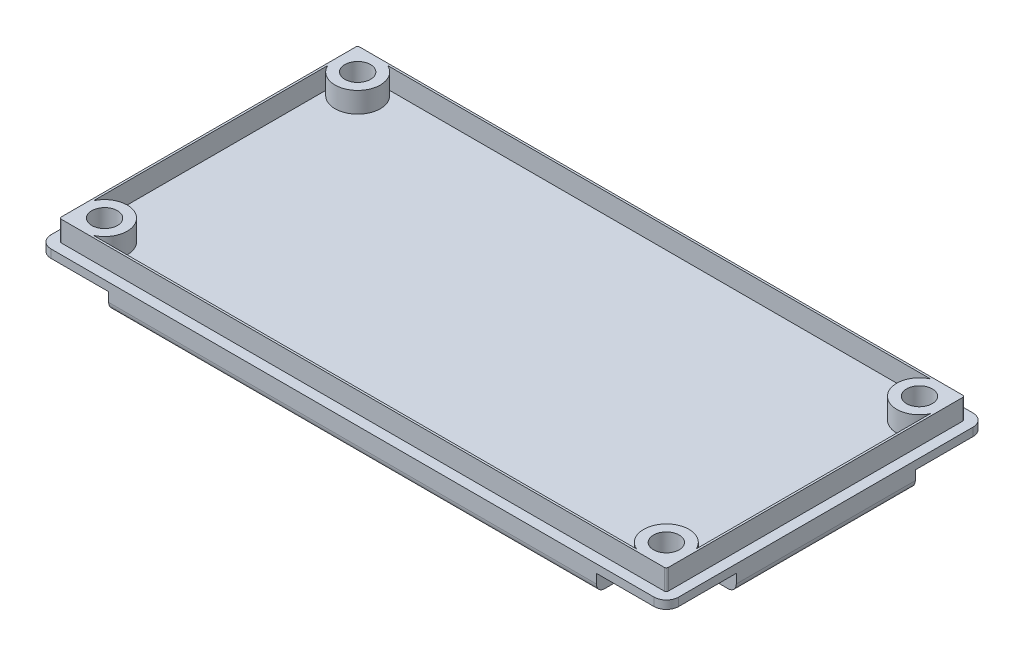
SolidWorks part; units mm, degrees
material "ABS"
ref_plane "Front Plane" through (0, 0, 0) normal (0, 0, 1) x (1, 0, 0)
ref_plane "Top Plane" through (0, 0, 0) normal (0, 1, 0) x (1, 0, 0)
ref_plane "Right Plane" through (0, 0, 0) normal (1, 0, 0) x (0, 0, -1)
sketch "Sketch1" plane through (0, 0, 0) normal (0, 1, 0) x (1, 0, 0)
  line L0 (-19.3675, 0) -> (19.3675, 0) construction
  line L1 (-18.6055, 9.8425) -> (18.6055, 9.8425)
  line L2 (-19.3675, 9.0805) -> (-19.3675, -9.0805)
  line L3 (-18.6055, -9.8425) -> (18.6055, -9.8425)
  line L4 (19.3675, 9.0805) -> (19.3675, -9.0805)
  line L5 (0, -9.8425) -> (0, 9.8425) construction
  line L8 (19.3675, 9.0805) -> (19.3675, -9.0805) construction
  line L9 (18.6055, -9.8425) -> (-18.6055, -9.8425) construction
  arc A0 (-18.6055, -9.8425) -> (-19.3675, -9.0805) centre (-18.6055, -9.0805) cw
  arc A1 (18.6055, -9.8425) -> (19.3675, -9.0805) centre (18.6055, -9.0805) ccw
  arc A2 (19.3675, 9.0805) -> (18.6055, 9.8425) centre (18.6055, 9.0805) ccw
  arc A3 (-19.3675, 9.0805) -> (-18.6055, 9.8425) centre (-18.6055, 9.0805) cw
  circle A4 centre (-17.3355, 7.8105) radius 0.7937
  circle A5 centre (17.3355, 7.8105) radius 0.7937
  circle A6 centre (17.3355, -7.8105) radius 0.7937
  circle A7 centre (-17.3355, -7.8105) radius 0.7937
  arc A9 (-19.3675, -9.0805) -> (-18.6055, -9.8425) centre (-18.6055, -9.0805) ccw construction
  circle A10 centre (17.3355, -7.8105) radius 0.7937 construction
extrude "Extrude1" add sketch "Sketch1" along normal blind 1.5875
fillet "Fillet2" radius 0.508 8 edges at (19.1443, 0, -9.6193) (19.3675, 0, 0) (19.1443, 0, 9.6193) (0, 0, 9.8425) (-19.1443, 0, 9.6193) (-19.3675, 0, 0) (-19.1443, 0, -9.6193) (0, 0, -9.8425)
sketch "Sketch2" plane through (0, 1.5875, 0) normal (0, 1, 0) x (-1, 0, 0)
  line L4 (-18.6055, -7.2285) -> (-18.6055, 7.2285)
  line L5 (-16.7535, 9.0805) -> (16.7535, 9.0805)
  line L6 (18.6055, 7.2285) -> (18.6055, -7.2285)
  line L7 (16.7535, -9.0805) -> (-16.7535, -9.0805)
  line L8 (18.6055, 9.2075) -> (-18.6055, 9.2075)
  line L9 (-18.7325, 9.0805) -> (-18.7325, -9.0805)
  line L10 (-18.6055, -9.2075) -> (18.6055, -9.2075)
  line L11 (18.7325, -9.0805) -> (18.7325, 9.0805)
  line L12 (18.6055, 9.2075) -> (-18.6055, 9.2075)
  line L13 (-18.7325, 9.0805) -> (-18.7325, -9.0805)
  line L14 (-18.6055, -9.2075) -> (18.6055, -9.2075)
  line L15 (18.7325, -9.0805) -> (18.7325, 9.0805)
  circle A4 centre (-17.3355, 7.8105) radius 0.7938 construction
  circle A5 centre (-17.3355, -7.8105) radius 0.7937 construction
  circle A6 centre (17.3355, -7.8105) radius 0.7937 construction
  circle A7 centre (17.3355, 7.8105) radius 0.7938 construction
  arc A8 (18.7325, 9.0805) -> (18.6055, 9.2075) centre (18.6055, 9.0805) ccw
  arc A9 (-18.6055, 9.2075) -> (-18.7325, 9.0805) centre (-18.6055, 9.0805) ccw
  arc A10 (-18.7325, -9.0805) -> (-18.6055, -9.2075) centre (-18.6055, -9.0805) ccw
  arc A11 (18.6055, -9.2075) -> (18.7325, -9.0805) centre (18.6055, -9.0805) ccw
  arc A12 (18.7325, 9.0805) -> (18.6055, 9.2075) centre (18.6055, 9.0805) ccw
  arc A13 (-18.6055, 9.2075) -> (-18.7325, 9.0805) centre (-18.6055, 9.0805) ccw
  arc A14 (-18.7325, -9.0805) -> (-18.6055, -9.2075) centre (-18.6055, -9.0805) ccw
  arc A15 (18.6055, -9.2075) -> (18.7325, -9.0805) centre (18.6055, -9.0805) ccw
  circle A16 centre (-17.3355, 7.8105) radius 0.7937
  circle A17 centre (-17.3355, -7.8105) radius 0.7937
  circle A18 centre (17.3355, -7.8105) radius 0.7937
  circle A19 centre (17.3355, 7.8105) radius 0.7937
  arc A20 (-16.7535, -9.0805) -> (-18.6055, -7.2285) centre (-17.3355, -7.8105) ccw
  arc A21 (16.7535, 9.0805) -> (18.6055, 7.2285) centre (17.3355, 7.8105) ccw
  arc A22 (18.6055, -7.2285) -> (16.7535, -9.0805) centre (17.3355, -7.8105) ccw
  arc A23 (-18.6055, 7.2285) -> (-16.7535, 9.0805) centre (-17.3355, 7.8105) ccw
  dimension "D1" = 0.635
extrude "Extrude2" add sketch "Sketch2" along normal blind 1.27
sketch "Sketch3" plane through (0, 0, 0) normal (0, -1, 0) x (1, 0, 0)
  line L0 (18.6055, -9.8425) -> (-18.6055, -9.8425) construction
  line L1 (-16.3195, -5.5245) -> (-19.3675, -5.5245)
  line L2 (-15.0495, -6.7945) -> (-15.0495, -9.8425)
  line L3 (-15.0495, -9.8425) -> (-19.3675, -9.8425)
  line L4 (-19.3675, -5.5245) -> (-19.3675, -9.8425)
  line L5 (-19.3675, -9.0805) -> (-19.3675, 9.0805) construction
  arc A1 (-15.0495, -6.7945) -> (-16.3195, -5.5245) centre (-16.3195, -6.7945) ccw
  point P10 (-15.0495, -5.5245)
  dimension "D1" = 1.27
  dimension "D2" = 4.318
extrude "Cut-Extrude1" cut sketch "Sketch3" against normal offset from surface (1.0795 mm away) 0.508 up to face at (0, 1.5875, 0)
mirror "Mirror1" about plane through (0, 0, 0) normal (1, 0, 0) of "Cut-Extrude1"
mirror "Mirror2" about plane through (0, 0, 0) normal (0, 0, 1) of "Cut-Extrude1", "Mirror1"
